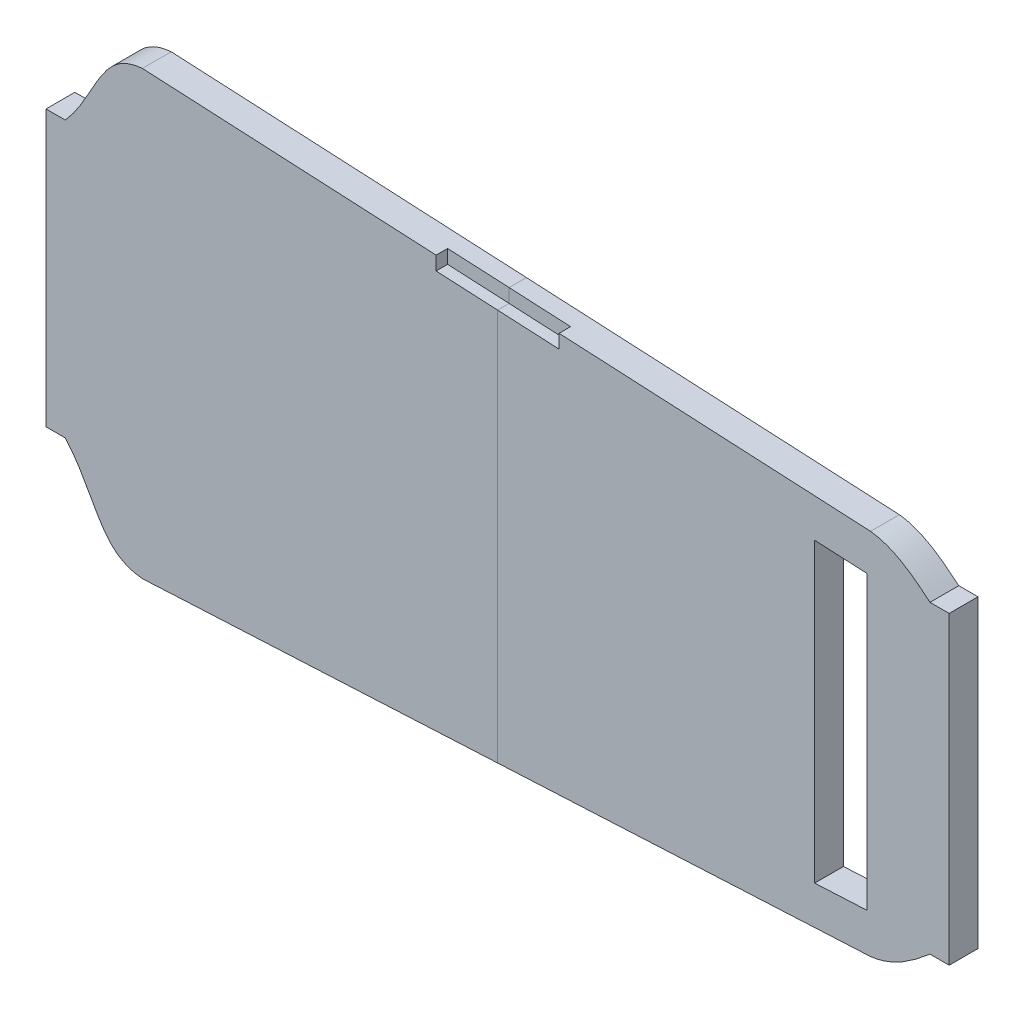
SolidWorks part; units mm, degrees
ref_plane "Front Plane" through (0, 0, 0) normal (0, 0, 1) x (1, 0, 0)
ref_plane "Top Plane" through (0, 0, 0) normal (0, 1, 0) x (1, 0, 0)
ref_plane "Right Plane" through (0, 0, 0) normal (1, 0, 0) x (0, 0, -1)
sketch "Sketch1" plane through (0, 0, 0) normal (0, 0, 1) x (1, 0, 0)
  line L0 (128.9591, 33.6286) -> (133.9591, 33.6286)
  line L1 (133.9591, 33.6286) -> (133.9591, -45.6561)
  line L2 (133.9591, -45.6561) -> (128.9591, -45.6561)
  line L3 (-96.0409, -41.8293) -> (-101.0409, -41.8293)
  line L4 (-101.0409, -41.8293) -> (-101.0409, 29.8017)
  line L5 (-101.0409, 29.8017) -> (-96.0409, 29.8017)
  line L41 (-75.9633, -63.5034) -> (113.4966, -53.9275)
  line L45 (113.4966, 41.9) -> (-75.9633, 51.476)
  spline S20 degree 3 poles (-96.0409, -41.8293) (-95.7989, -42.0932) (-95.562, -42.3621) (-94.0395, -44.1568) (-92.9236, -45.7924) (-90.8585, -49.1709) (-89.9111, -50.915) (-88.4578, -53.5103) (-87.9675, -54.372) (-86.9409, -56.0639) (-86.4049, -56.8943) (-85.5307, -58.0913) (-85.2274, -58.4821) (-84.5888, -59.2416) (-84.2542, -59.6091) (-83.2049, -60.6516) (-82.4406, -61.2706) (-81.1606, -62.0427) (-80.7193, -62.2694) (-79.8173, -62.6609) (-79.3554, -62.8265) (-77.9405, -63.2433) (-76.9542, -63.4142) (-75.9633, -63.5034) knots 0.352672 0.352672 0.352672 0.352672 0.375 0.375 0.5 0.5 0.625 0.625 0.6875 0.6875 0.75 0.75 0.78125 0.78125 0.8125 0.8125 0.875 0.875 0.90625 0.90625 0.9375 0.9375 1 1 1 1
  spline S21 degree 3 poles (113.4966, -53.9275) (114.9739, -53.7603) (116.3895, -53.4083) (118.4389, -52.6587) (119.1098, -52.372) (120.4306, -51.7359) (121.0829, -51.3848) (122.9889, -50.2675) (124.1972, -49.4372) (126.5417, -47.6779) (127.6776, -46.7485) (128.8505, -45.7489) (128.9048, -45.7025) (128.9591, -45.6561) knots 0 0 0 0 0.125 0.125 0.1875 0.1875 0.25 0.25 0.375 0.375 0.5 0.5 0.506074 0.506074 0.506074 0.506074
  spline S22 degree 3 poles (128.9591, 33.6286) (128.9134, 33.6677) (127.7512, 34.6604) (126.5688, 35.629) (124.8053, 36.9539) (124.207, 37.3838) (122.9921, 38.2061) (122.3746, 38.5993) (120.4843, 39.7099) (119.1742, 40.3597) (117.0932, 41.1246) (116.3871, 41.3415) (114.9575, 41.6873) (114.2325, 41.8167) (113.4966, 41.9) knots 0.494879 0.494879 0.494879 0.494879 0.5 0.625 0.625 0.6875 0.6875 0.75 0.75 0.875 0.875 0.9375 0.9375 1 1 1 1
  spline S23 degree 3 poles (-75.9633, 51.476) (-76.9698, 51.3853) (-77.9567, 51.2137) (-79.3959, 50.7857) (-79.8697, 50.6139) (-80.7968, 50.2046) (-81.2406, 49.9713) (-82.0898, 49.4495) (-82.4952, 49.1609) (-83.2715, 48.5337) (-83.643, 48.1944) (-84.7084, 47.1168) (-85.3332, 46.3434) (-86.4913, 44.7377) (-87.0238, 43.9049) (-88.0449, 42.211) (-88.533, 41.3497) (-89.9829, 38.7563) (-90.9324, 37.0136) (-92.9995, 33.6504) (-94.1146, 32.0312) (-95.6034, 30.2877) (-95.8197, 30.0429) (-96.0409, 29.8017) knots 0 0 0 0 0.0625 0.0625 0.09375 0.09375 0.125 0.125 0.15625 0.15625 0.1875 0.1875 0.25 0.25 0.3125 0.3125 0.375 0.375 0.5 0.5 0.625 0.625 0.645749 0.645749 0.645749 0.645749
  dimension "D2" = 5
  dimension "D3" = 235
  dimension "D1" = 5
extrude "Boss-Extrude1" add sketch "Sketch1" along normal blind 7.5
sketch "Sketch3" plane through (0, 0, 7.5) normal (0, 0, 1) x (1, 0, 0)
  line L8 (98.9591, 32.622) -> (98.9591, -44.6495)
  line L9 (112.6163, 31.9317) -> (112.616, -43.9592)
  line L16 (-91.0409, 20.4585) -> (-91.0409, -32.4859)
  line L17 (-75.6152, -53.4731) -> (112.616, -43.9592)
  line L18 (123.9591, -36.7736) -> (123.9591, 24.7461)
  line L19 (112.6163, 31.9317) -> (-75.617, 41.4457)
  line L21 (98.9591, -44.6495) -> (112.616, -43.9592)
  line L23 (112.6163, 31.9317) -> (98.9591, 32.622)
  spline S8 degree 3 poles (-321.0775, 1010.8366) (-47.2339, 7.6147) (-67.1052, 43.8663) (-76.1572, 41.3178) (-76.2916, 41.2718) (-76.5307, 41.1314) (-76.6353, 41.0425) (-76.8379, 40.8568) (-76.9347, 40.7578) (-77.2149, 40.454) (-77.3881, 40.2415) (-77.721, 39.8065) (-77.8806, 39.5839) (-78.3463, 38.9067) (-78.6393, 38.4418) (-79.2081, 37.5024) (-79.4837, 37.0276) (-80.2986, 35.5963) (-80.8274, 34.6336) (-81.9003, 32.7171) (-82.4434, 31.7627) (-83.5708, 29.8782) (-84.1563, 28.9469) (-85.3832, 27.1256) (-86.0236, 26.2372) (-87.0339, 24.9455) (-87.3789, 24.5217) (-88.0869, 23.689) (-88.4519, 23.2816) (-314.8584, -223.5955) (-540.895, -470.0693) (-766.9317, -716.5431) knots -1.028377 -1.028377 -1.028377 -1.028377 0.015625 0.015625 0.03125 0.03125 0.046875 0.046875 0.0625 0.0625 0.09375 0.09375 0.125 0.125 0.1875 0.1875 0.25 0.25 0.375 0.375 0.5 0.5 0.625 0.625 0.75 0.75 0.8125 0.8125 0.875 0.875 39.07131 39.07131 39.07131 39.07131 only from (-75.617, 41.4457) to (-91.0409, 20.4585)
  spline S9 degree 3 poles (-766.9054, 704.5399) (-540.8771, 458.0575) (-314.8488, 211.5752) (-88.4504, -35.3108) (-88.0852, -35.7184) (-87.3766, -36.552) (-87.0312, -36.9762) (-86.0196, -38.2696) (-85.3777, -39.1604) (-84.15, -40.9839) (-83.566, -41.9136) (-82.4391, -43.7975) (-81.8962, -44.7517) (-80.8236, -46.6681) (-80.2947, -47.6306) (-79.4797, -49.0619) (-79.2041, -49.5367) (-78.635, -50.476) (-78.342, -50.9409) (-77.8751, -51.6192) (-77.7149, -51.8423) (-77.3803, -52.2781) (-77.2066, -52.4906) (-76.9273, -52.7929) (-76.8307, -52.8914) (-76.6276, -53.0763) (-76.523, -53.1647) (-76.2842, -53.3022) (-76.1512, -53.3474) (-67.4145, -55.7808) (-48.6593, -21.9352) (-319.6352, -1022.5263) knots -38.048556 -38.048556 -38.048556 -38.048556 0.125 0.125 0.1875 0.1875 0.25 0.25 0.375 0.375 0.5 0.5 0.625 0.625 0.75 0.75 0.8125 0.8125 0.875 0.875 0.90625 0.90625 0.9375 0.9375 0.953125 0.953125 0.96875 0.96875 0.984375 0.984375 1.999332 1.999332 1.999332 1.999332 only from (-91.0409, -32.4859) to (-75.6152, -53.4731)
  spline S10 degree 3 poles (-281.2869, 875.1918) (59.9439, -6.2836) (96.2316, -49.9984) (114.7851, -43.3509) (115.2983, -43.1191) (116.3047, -42.6001) (116.7962, -42.3135) (117.7546, -41.7096) (118.223, -41.3909) (119.6055, -40.4004) (120.496, -39.6971) (121.8054, -38.6138) (122.237, -38.2468) (376.3954, 179.1728) (630.1232, 396.2241) (883.8511, 613.2754) knots -4.136795 -4.136795 -4.136795 -4.136795 0.125 0.125 0.25 0.25 0.375 0.375 0.5 0.5 0.75 0.75 0.875 0.875 74.543314 74.543314 74.543314 74.543314 only from (112.616, -43.9592) to (123.9591, -36.7736)
  spline S11 degree 3 poles (883.847, -625.308) (630.1203, -408.2548) (376.3938, -191.2018) (122.2365, 26.2197) (121.8048, 26.5868) (120.495, 27.6705) (119.6039, 28.3743) (118.2218, 29.3639) (117.7535, 29.6824) (116.7951, 30.2867) (116.3031, 30.5737) (115.2983, 31.092) (114.7855, 31.3232) (96.4332, 37.8999) (60.4545, -4.4095) (-287.7125, -884.1076) knots -73.522553 -73.522553 -73.522553 -73.522553 0.125 0.125 0.25 0.25 0.5 0.5 0.625 0.625 0.75 0.75 0.875 0.875 5.091372 5.091372 5.091372 5.091372 only from (123.9591, 24.7461) to (112.6163, 31.9317)
  dimension "D3" = 13.6572
  dimension "D1" = 10
extrude "Cut-Extrude1" cut sketch "Sketch3" against normal through all
sketch "Sketch5" plane through (0, 0, 7.5) normal (0, 0, 1) x (1, 0, 0)
  line L0 (16.4591, 55.5543) -> (16.4591, -65.458)
  line L1 (-101.0409, 29.8017) -> (-101.0409, -41.8293) construction
  line L2 (0.4591, 47.6133) -> (0.4591, 44.0381)
  line L3 (113.4966, 41.9) -> (-75.9633, 51.476) construction
  line L4 (0.4591, 44.0381) -> (32.4591, 42.4207)
  line L5 (32.4591, 42.4207) -> (32.4591, 45.9959)
  line L8 (0.4591, 47.6133) -> (32.4591, 45.9959)
  dimension "D1" = 117.5
  dimension "D2" = 16
  dimension "D3" = 16
  dimension "D4" = 3.5752
  dimension "D5" = 3.5752
extrude "Cut-Extrude3" cut sketch "Sketch5" against normal blind 3 contours L8 L5 L4 L2
sketch "Sketch6" plane through (0, 0, 7.5) normal (0, 0, 1) x (1, 0, 0)
  line L0 (16.4591, 62.9424) -> (16.4591, -80.7163)
  line L1 (-101.0409, 29.8017) -> (-101.0409, -41.8293) construction
  dimension "D1" = 117.5
split "Split2" trim tools "Sketch6" bodies to split 110 resulting bodies 111 112
